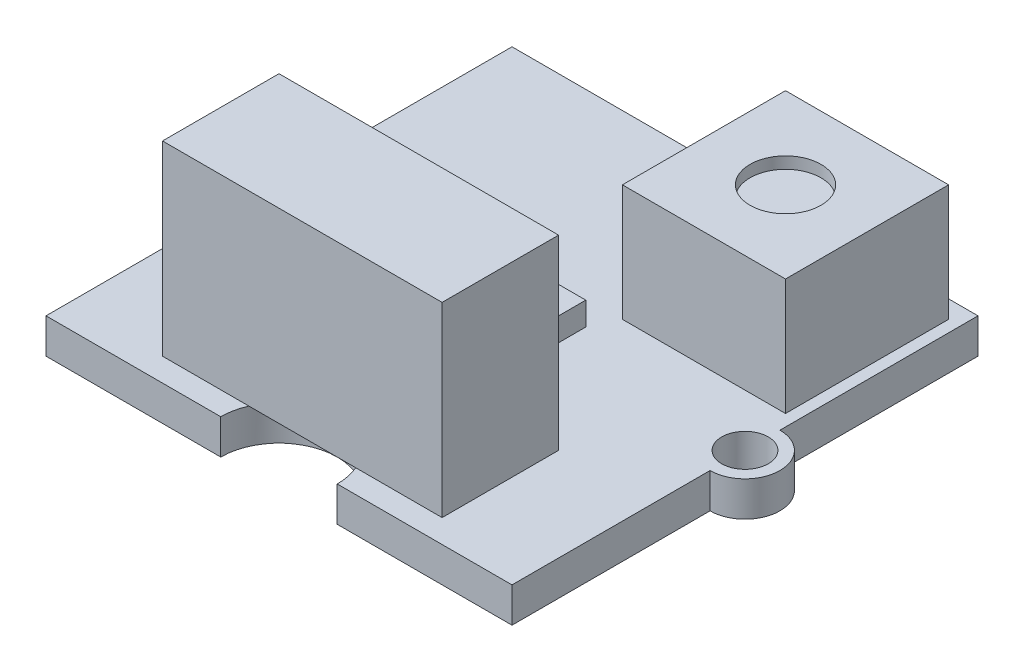
SolidWorks part; units mm, degrees
ref_plane "Front Plane" through (0, 0, 0) normal (0, 0, 1) x (1, 0, 0)
ref_plane "Top Plane" through (0, 0, 0) normal (0, 1, 0) x (1, 0, 0)
ref_plane "Right Plane" through (0, 0, 0) normal (1, 0, 0) x (0, 0, -1)
sketch "Sketch2" plane through (0, 0, 0) normal (0, 1, 0) x (1, 0, 0)
  line L1 (-10, 10) -> (10, 10)
  line L2 (-10, 10) -> (-10, -10)
  line L3 (-10, -10) -> (10, -10)
  line L4 (10, 10) -> (10, -10)
  line L5 (-10, 10) -> (10, -10) construction
  line L6 (-10, -10) -> (10, 10) construction
  point P0 (0, 0)
  dimension "D1" = 20
  dimension "D2" = 20
extrude "pcb" add sketch "Sketch2" along normal blind 1.5
sketch "Sketch3" plane through (0, 1.5, 0) normal (0, 1, 0) x (1, 0, 0)
  line L0 (-10, 10) -> (-10, -10) construction
  line L1 (10, -10) -> (10, 10) construction
  circle A0 centre (-10, 0) radius 1.5
  circle A1 centre (10, 0) radius 1.5
  dimension "D1" = 3
  dimension "D2" = 3
extrude "side mounting holes frame" add sketch "Sketch3" against normal blind 1.5
sketch "Sketch4" plane through (0, 1.5, 0) normal (0, 1, 0) x (1, 0, 0)
  circle A0 centre (-10, 0) radius 1
  circle A1 centre (10, 0) radius 1
  dimension "D1" = 2
  dimension "D2" = 2
extrude "side mounting holes" cut sketch "Sketch4" against normal blind 1.5
sketch "Sketch5" plane through (0, 1.5, 0) normal (0, 1, 0) x (1, 0, 0)
  line L0 (10, 10) -> (-10, 10) construction
  line L1 (-10, -10) -> (10, -10) construction
  circle A0 centre (0, 10) radius 2.5
  circle A1 centre (0, -10) radius 2.5
  dimension "D1" = 5
  dimension "D2" = 5
extrude "side inlets" cut sketch "Sketch5" against normal blind 1.5
sketch "Sketch6" plane through (0, 1.5, 0) normal (0, 1, 0) x (1, 0, 0)
  line L0 (-10, -1.5) -> (-10, -10) construction
  line L1 (-6, -4) -> (6, -4)
  line L2 (-6, -4) -> (-6, -9)
  line L3 (-6, -9) -> (6, -9)
  line L4 (6, -4) -> (6, -9)
  line L5 (-6, -4) -> (6, -9) construction
  line L6 (-6, -9) -> (6, -4) construction
  line L7 (2.5, -10) -> (10, -10) construction
  point P0 (0, -6.5)
  dimension "D1" = 12
  dimension "D2" = 4
  dimension "D3" = 5
  dimension "D4" = 1
extrude "Boss-Extrude3" add sketch "Sketch6" along normal blind 8
sketch "Sketch7" plane through (0, 1.5, 0) normal (0, 1, 0) x (1, 0, 0)
  line L0 (-10, 10) -> (-10, 1.5) construction
  line L1 (2.5, 9.2388) -> (9.5, 9.2388)
  line L2 (2.5, 9.2388) -> (2.5, 2.2388)
  line L3 (2.5, 2.2388) -> (9.5, 2.2388)
  line L4 (9.5, 9.2388) -> (9.5, 2.2388)
  line L5 (2.5, 9.2388) -> (9.5, 2.2388) construction
  line L6 (2.5, 2.2388) -> (9.5, 9.2388) construction
  point P0 (6, 5.7388)
  dimension "D1" = 7
  dimension "D2" = 7
  dimension "D3" = 12.5
extrude "Boss-Extrude4" add sketch "Sketch7" along normal blind 5
sketch "Sketch8" plane through (0, 6.5, 0) normal (0, 1, 0) x (1, 0, 0)
  line L0 (2.5, 2.2388) -> (9.5, 2.2388) construction
  line L1 (2.5, 9.2388) -> (2.5, 2.2388) construction
  circle A0 centre (6, 5.7388) radius 1.5227
  dimension "D1" = 3.5
  dimension "D2" = 3.5
extrude "Cut-Extrude3" cut sketch "Sketch8" against normal blind 0.5
sketch "Sketch9" plane through (0, 1.5, 0) normal (0, 1, 0) x (1, 0, 0)
  line L0 (-10, -1.5) -> (-10, -10) construction
  line L1 (-3, 1.1672) -> (2, 1.1672)
  line L2 (-3, 1.1672) -> (-3, -2.3328)
  line L3 (-3, -2.3328) -> (2, -2.3328)
  line L4 (2, 1.1672) -> (2, -2.3328)
  line L5 (-3, 1.1672) -> (2, -2.3328) construction
  line L6 (-3, -2.3328) -> (2, 1.1672) construction
  point P0 (-0.5, -0.5828)
  dimension "D1" = 5
  dimension "D2" = 3.5
  dimension "D3" = 7
extrude "Boss-Extrude5" add sketch "Sketch9" along normal blind 1
